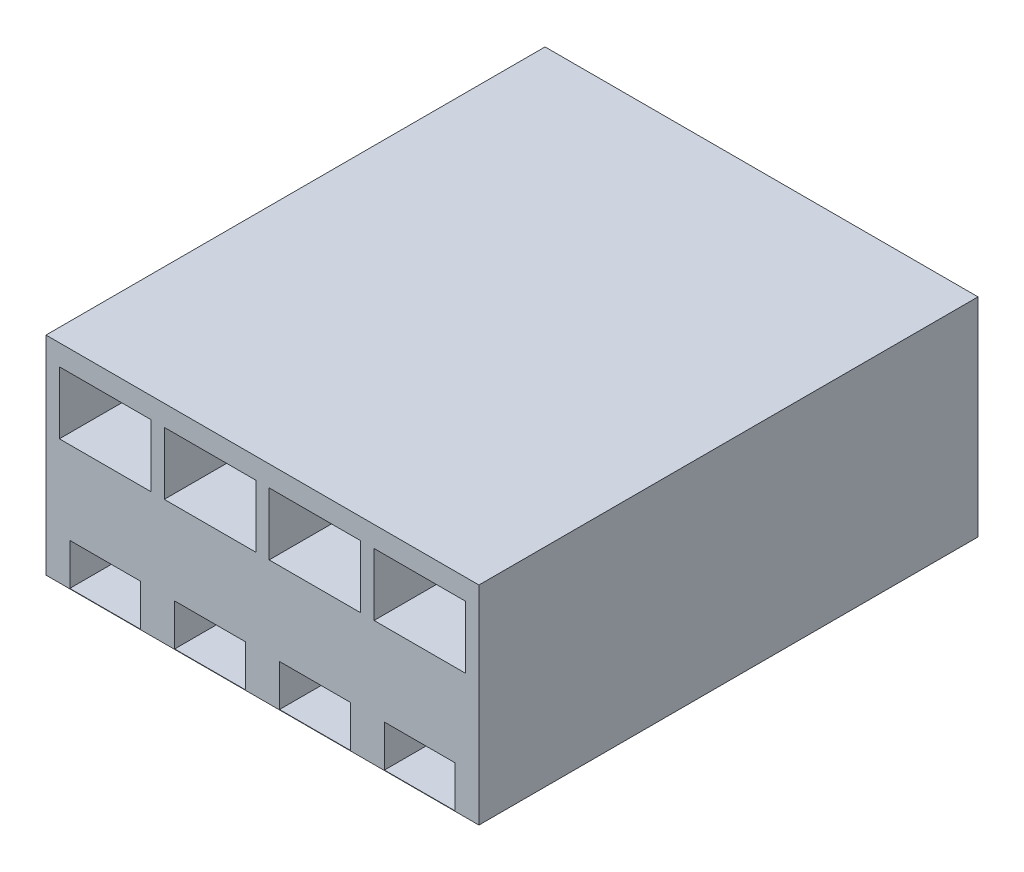
SolidWorks part; units mm, degrees
ref_plane "Front Plane" through (0, 0, 0) normal (0, 0, 1) x (1, 0, 0)
ref_plane "Top Plane" through (0, 0, 0) normal (0, 1, 0) x (1, 0, 0)
ref_plane "Right Plane" through (0, 0, 0) normal (1, 0, 0) x (0, 0, -1)
sketch "Sketch2" plane through (0, 0, 0) normal (0, 0, 1) x (1, 0, 0)
  line L1 (1.194, 0.1359) -> (11.604, 0.1359)
  line L2 (1.194, 0.1359) -> (1.194, -4.8641)
  line L3 (1.194, -4.8641) -> (11.604, -4.8641)
  line L4 (11.604, 0.1359) -> (11.604, -4.8641)
  line L5 (1.194, 0.1359) -> (11.604, -4.8641) construction
  line L6 (1.194, -4.8641) -> (11.604, 0.1359) construction
  line L10 (9.332, -3.8541) -> (11.032, -3.8541)
  line L11 (1.766, -3.8541) -> (3.466, -3.8541)
  line L12 (9.082, -0.3641) -> (11.282, -0.3641)
  line L13 (1.516, -0.3641) -> (3.716, -0.3641)
  line L14 (1.516, -0.3641) -> (1.516, -1.8641)
  line L15 (1.516, -1.8641) -> (3.716, -1.8641)
  line L16 (3.716, -0.3641) -> (3.716, -1.8641)
  line L17 (1.516, -0.3641) -> (3.716, -1.8641) construction
  line L18 (1.516, -1.8641) -> (3.716, -0.3641) construction
  line L19 (9.082, -0.3641) -> (9.082, -1.8641)
  line L20 (9.082, -1.8641) -> (11.282, -1.8641)
  line L21 (11.282, -0.3641) -> (11.282, -1.8641)
  line L22 (9.082, -0.3641) -> (11.282, -1.8641) construction
  line L23 (9.082, -1.8641) -> (11.282, -0.3641) construction
  line L24 (6.56, -0.3641) -> (8.76, -0.3641)
  line L25 (6.56, -0.3641) -> (6.56, -1.8641)
  line L26 (6.56, -1.8641) -> (8.76, -1.8641)
  line L27 (8.76, -0.3641) -> (8.76, -1.8641)
  line L28 (6.56, -0.3641) -> (8.76, -1.8641) construction
  line L29 (6.56, -1.8641) -> (8.76, -0.3641) construction
  line L30 (4.038, -0.3641) -> (6.238, -0.3641)
  line L31 (4.038, -0.3641) -> (4.038, -1.8641)
  line L32 (4.038, -1.8641) -> (6.238, -1.8641)
  line L33 (6.238, -0.3641) -> (6.238, -1.8641)
  line L34 (4.038, -0.3641) -> (6.238, -1.8641) construction
  line L35 (4.038, -1.8641) -> (6.238, -0.3641) construction
  line L36 (1.766, -3.8541) -> (1.766, -4.8541)
  line L37 (1.766, -4.8541) -> (3.466, -4.8541)
  line L38 (3.466, -3.8541) -> (3.466, -4.8541)
  line L39 (4.288, -3.8541) -> (5.988, -3.8541)
  line L40 (4.288, -3.8541) -> (4.288, -4.8541)
  line L41 (4.288, -4.8541) -> (5.988, -4.8541)
  line L42 (5.988, -3.8541) -> (5.988, -4.8541)
  line L43 (6.81, -3.8541) -> (8.51, -3.8541)
  line L44 (6.81, -3.8541) -> (6.81, -4.8541)
  line L45 (6.81, -4.8541) -> (8.51, -4.8541)
  line L46 (8.51, -3.8541) -> (8.51, -4.8541)
  line L51 (9.332, -3.8541) -> (9.332, -4.8541)
  line L52 (9.332, -4.8541) -> (11.032, -4.8541)
  line L53 (11.032, -3.8541) -> (11.032, -4.8541)
  point P0 (6.399, -2.3641)
  point P10 (2.616, -1.1141)
  point P15 (10.182, -1.1141)
  point P20 (7.66, -1.1141)
  point P25 (5.138, -1.1141)
  point P41 (0, 0)
  point P42 (24.0548, -18.0988)
  point P43 (23.8698, -18.1366)
  dimension "D1" = 10.41
  dimension "D2" = 5
  dimension "D3" = 0.25
  dimension "D4" = 0.25
  dimension "D5" = 2.2
  dimension "D6" = 2.2
  dimension "D7" = 2.2
  dimension "D8" = 2.2
  dimension "D9" = 0.322
  dimension "D10" = 0.322
  dimension "D11" = 0.322
  dimension "D12" = 0.322
  dimension "D13" = 0.5
  dimension "D14" = 1.5
  dimension "D15" = 1.5
  dimension "D16" = 1.5
  dimension "D17" = 1.5
  dimension "D18" = 0.5
  dimension "D19" = 0.5
  dimension "D20" = 0.5
  dimension "D21" = 0.01
  dimension "D22" = 1
  dimension "D23" = 1
  dimension "D24" = 1
  dimension "D25" = 0.25
  dimension "D26" = 0.25
  dimension "D27" = 0.25
  dimension "D28" = 0.25
  dimension "D29" = 0.25
  dimension "D30" = 0.25
extrude "Boss-Extrude1" add sketch "Sketch2" along normal blind 12
sketch "Sketch3" plane through (0, 0, 0) normal (0, 0, 1) x (1, 0, 0)
  line L1 (1.194, 0.1359) -> (11.604, 0.1359)
  line L2 (1.194, 0.1359) -> (1.194, -4.8641)
  line L3 (1.194, -4.8641) -> (11.604, -4.8641)
  line L4 (11.604, 0.1359) -> (11.604, -4.8641)
  line L5 (1.194, 0.1359) -> (11.604, -4.8641) construction
  line L6 (1.194, -4.8641) -> (11.604, 0.1359) construction
  line L10 (11.604, 0.1359) -> (1.194, 0.1359) construction
  line L11 (11.604, -4.8641) -> (11.604, 0.1359) construction
  line L12 (9.082, -0.3641) -> (11.282, -0.3641)
  line L13 (1.516, -0.3641) -> (3.716, -0.3641)
  line L14 (1.516, -0.3641) -> (1.516, -1.8641)
  line L15 (1.516, -1.8641) -> (3.716, -1.8641)
  line L16 (3.716, -0.3641) -> (3.716, -1.8641)
  line L17 (1.516, -0.3641) -> (3.716, -1.8641) construction
  line L18 (1.516, -1.8641) -> (3.716, -0.3641) construction
  line L19 (9.082, -0.3641) -> (9.082, -1.8641)
  line L20 (9.082, -1.8641) -> (11.282, -1.8641)
  line L21 (11.282, -0.3641) -> (11.282, -1.8641)
  line L22 (9.082, -0.3641) -> (11.282, -1.8641) construction
  line L23 (9.082, -1.8641) -> (11.282, -0.3641) construction
  line L24 (6.56, -0.3641) -> (8.76, -0.3641)
  line L25 (6.56, -0.3641) -> (6.56, -1.8641)
  line L26 (6.56, -1.8641) -> (8.76, -1.8641)
  line L27 (8.76, -0.3641) -> (8.76, -1.8641)
  line L28 (6.56, -0.3641) -> (8.76, -1.8641) construction
  line L29 (6.56, -1.8641) -> (8.76, -0.3641) construction
  line L30 (4.038, -0.3641) -> (6.238, -0.3641)
  line L31 (4.038, -0.3641) -> (4.038, -1.8641)
  line L32 (4.038, -1.8641) -> (6.238, -1.8641)
  line L33 (6.238, -0.3641) -> (6.238, -1.8641)
  line L34 (4.038, -0.3641) -> (6.238, -1.8641) construction
  line L35 (4.038, -1.8641) -> (6.238, -0.3641) construction
  line L36 (9.332, -3.8541) -> (11.032, -3.8541)
  line L37 (1.766, -3.8541) -> (3.466, -3.8541)
  line L38 (1.766, -3.8541) -> (1.766, -4.8641)
  line L39 (1.766, -4.8641) -> (3.466, -4.8641)
  line L40 (3.466, -3.8541) -> (3.466, -4.8641)
  line L41 (4.288, -3.8541) -> (5.988, -3.8541)
  line L42 (4.288, -3.8541) -> (4.288, -4.8641)
  line L43 (4.288, -4.8641) -> (5.988, -4.8641)
  line L44 (5.988, -3.8541) -> (5.988, -4.8641)
  line L45 (6.81, -3.8541) -> (8.51, -3.8541)
  line L46 (6.81, -3.8541) -> (6.81, -4.8641)
  line L47 (6.81, -4.8641) -> (8.51, -4.8641)
  line L48 (8.51, -3.8541) -> (8.51, -4.8641)
  line L49 (9.332, -3.8541) -> (9.332, -4.8641)
  line L50 (9.332, -4.8641) -> (11.032, -4.8641)
  line L51 (11.032, -3.8541) -> (11.032, -4.8641)
  line L52 (11.032, -3.8541) -> (9.332, -3.8541) construction
  line L53 (8.51, -3.8541) -> (6.81, -3.8541) construction
  line L54 (5.988, -3.8541) -> (4.288, -3.8541) construction
  line L55 (3.466, -3.8541) -> (1.766, -3.8541) construction
  line L56 (11.032, -4.8541) -> (11.032, -3.8541) construction
  line L57 (9.332, -3.8541) -> (9.332, -4.8541) construction
  line L58 (8.51, -4.8541) -> (8.51, -3.8541) construction
  line L59 (6.81, -3.8541) -> (6.81, -4.8541) construction
  line L60 (5.988, -4.8541) -> (5.988, -3.8541) construction
  line L61 (4.288, -3.8541) -> (4.288, -4.8541) construction
  line L62 (3.466, -4.8541) -> (3.466, -3.8541) construction
  line L63 (1.766, -3.8541) -> (1.766, -4.8541) construction
  line L65 (11.032, -3.8541) -> (9.332, -3.8541)
  line L66 (11.032, -3.8541) -> (11.032, -4.8641)
  line L67 (11.032, -4.8641) -> (9.332, -4.8641)
  line L68 (9.332, -3.8541) -> (9.332, -4.8641)
  line L69 (8.51, -3.8541) -> (6.81, -3.8541)
  line L70 (8.51, -3.8541) -> (8.51, -4.8641)
  line L71 (8.51, -4.8641) -> (6.81, -4.8641)
  line L72 (6.81, -3.8541) -> (6.81, -4.8641)
  line L73 (5.988, -3.8541) -> (4.288, -3.8541)
  line L74 (5.988, -3.8541) -> (5.988, -4.8641)
  line L75 (5.988, -4.8641) -> (4.288, -4.8641)
  line L76 (4.288, -3.8541) -> (4.288, -4.8641)
  line L77 (3.466, -3.8541) -> (1.766, -3.8541)
  line L78 (3.466, -3.8541) -> (3.466, -4.8641)
  line L79 (3.466, -4.8641) -> (1.766, -4.8641)
  line L80 (1.766, -3.8541) -> (1.766, -4.8641)
  point P0 (6.399, -2.3641)
  point P10 (2.616, -1.1141)
  point P15 (10.182, -1.1141)
  point P20 (7.66, -1.1141)
  point P25 (5.138, -1.1141)
  dimension "D1" = 10.41
  dimension "D2" = 5
  dimension "D5" = 2.2
  dimension "D6" = 2.2
  dimension "D7" = 2.2
  dimension "D8" = 2.2
  dimension "D9" = 0.322
  dimension "D10" = 0.322
  dimension "D11" = 0.322
  dimension "D12" = 0.322
  dimension "D13" = 0.5
  dimension "D14" = 1.5
  dimension "D15" = 1.5
  dimension "D16" = 1.5
  dimension "D17" = 1.5
  dimension "D18" = 0.5
  dimension "D19" = 0.5
  dimension "D20" = 0.5
extrude "Boss-Extrude10" add sketch "Sketch3" along normal blind 5 contours L21 L12 L19 L20 | L27 L24 L25 L26 | L33 L30 L31 L32 | L16 L13 L14 L15 | L44 L41 L42 L43 | L40 L37 L38 L39 | L48 L45 L46 L47 | L51 L36 L49 L50
